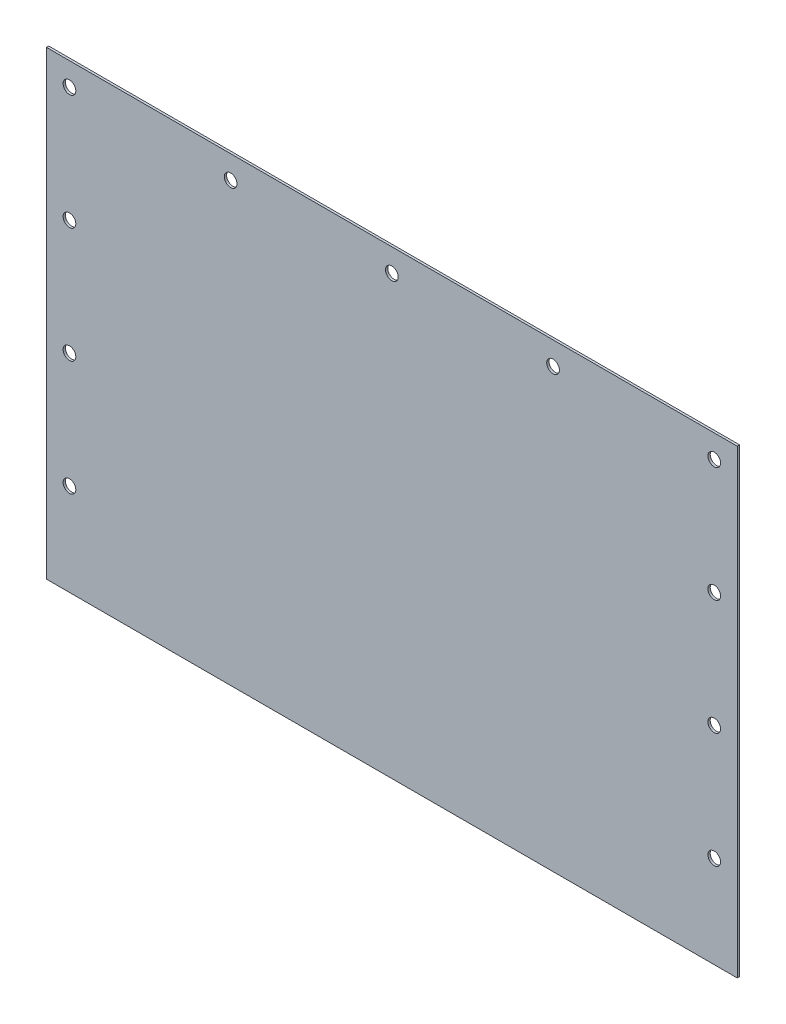
SolidWorks part; units mm, degrees
ref_plane "정면" through (0, 0, 0) normal (0, 0, 1) x (1, 0, 0)
ref_plane "윗면" through (0, 0, 0) normal (0, 1, 0) x (1, 0, 0)
ref_plane "우측면" through (0, 0, 0) normal (1, 0, 0) x (0, 0, -1)
sketch "스케치1" plane through (0, 0, 0) normal (0, 0, 1) x (1, 0, 0)
  line L1 (-150, -110) -> (150, -110)
  line L2 (-150, -110) -> (-150, 110)
  line L3 (-150, 110) -> (150, 110)
  line L4 (150, -110) -> (150, 110)
  line L5 (-150, -110) -> (150, 110) construction
  line L6 (-150, 110) -> (150, -110) construction
  line L7 (-140, -100) -> (140, -100) construction
  line L8 (-140, -100) -> (-140, 100) construction
  line L9 (-140, 100) -> (140, 100) construction
  line L10 (140, -100) -> (140, 100) construction
  line L11 (-140, -100) -> (140, 100) construction
  line L12 (-140, 100) -> (140, -100) construction
  point P0 (0, 0)
  point P6 (0, 0)
  point P12 (-140, 100)
  point P13 (140, 100)
  point P14 (140, -100)
  point P15 (-140, -100)
  point P16 (0, -100)
  point P17 (-70, -100)
  point P19 (70, -100)
  point P20 (-140, -50)
  point P22 (0, 100)
  point P23 (-70, 100)
  point P25 (70, 100)
  point P26 (-140, 0)
  point P27 (0, 100)
  point P29 (-140, 50)
  point P32 (140, -50)
  point P33 (140, 0)
  point P35 (140, 50)
  dimension "D1" = 300
  dimension "D2" = 220
  dimension "D3" = 10
  dimension "D4" = 10
  dimension "D5" = 50
  dimension "D6" = 50
  dimension "D7" = 70
  dimension "D8" = 70
extrude "보스-돌출1" add sketch "스케치1" along normal blind 1 contours L3 L4 L1 L2
hole_wizard "M5 여유 구멍1" positions "스케치2" profile "스케치3" hole size "M5" standard "KS" end condition through all
sketch "스케치2" plane through (0, 0, 0) normal (0, 0, -1) x (-1, 0, 0)
  point P0 (-140, 100)
  point P3 (-70, 100)
  point P6 (70, 100)
  point P9 (0, 100)
  point P18 (140, 100)
  point P21 (140, 50)
  point P24 (140, -50)
  point P27 (140, 0)
  point P36 (140, -100)
  point P39 (-140, 50)
  point P42 (-140, -50)
  point P45 (-140, 0)
  point P54 (-140, -100)
  point P57 (-70, -100)
  point P60 (70, -100)
  point P63 (0, -100)
sketch "스케치3" plane through (140, 100, 0) normal (1, 0, 0) x (0, 1, 0)
  line L0 (0, 0) -> (0, 1)
  line L1 (0, 1) -> (2.75, 1)
  line L2 (2.75, 1) -> (2.75, 0)
  line L5 (2.75, 0) -> (0, 0)
  line L11 (0, -6.35) -> (0, 107.95) construction
  dimension "관통 구멍 지름" = 5.5
  dimension "관통 구멍 깊이" = 1
sketch "스케치4" plane through (0, 0, 1) normal (0, 0, 1) x (1, 0, 0)
  line L0 (150, -110) -> (150, 110) construction
  line L1 (-150, -110) -> (150, -110)
  line L2 (-150, -110) -> (-150, -90)
  line L3 (-150, -90) -> (150, -90)
  line L4 (150, -110) -> (150, -90)
  line L5 (-150, -110) -> (150, -90) construction
  line L6 (-150, -90) -> (150, -110) construction
  line L7 (-235, -90) -> (235, -90) construction
  point P4 (0, -100)
extrude "컷-돌출1" cut sketch "스케치4" against normal blind 10
